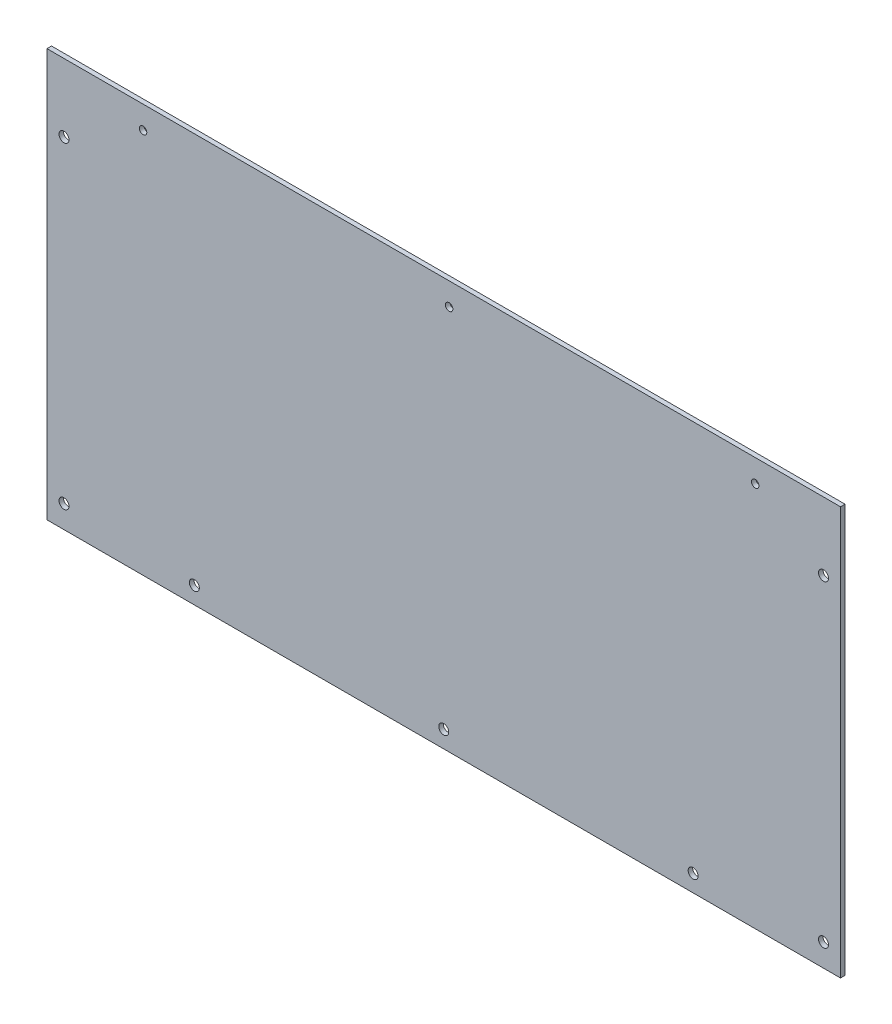
SolidWorks part; units mm, degrees
ref_plane "正面" through (0, 0, 0) normal (0, 0, 1) x (1, 0, 0)
ref_plane "平面" through (0, 0, 0) normal (0, 1, 0) x (1, 0, 0)
ref_plane "右側面" through (0, 0, 0) normal (1, 0, 0) x (0, 0, -1)
sketch "ｽｹｯﾁ1" plane through (0, 0, 0) normal (0, 0, 1) x (1, 0, 0)
  line L1 (-175, 90) -> (175, 90)
  line L2 (-175, 90) -> (-175, -90)
  line L3 (-175, -90) -> (175, -90)
  line L4 (175, 90) -> (175, -90)
  line L5 (-175, 90) -> (175, -90) construction
  line L6 (-175, -90) -> (175, 90) construction
  point P0 (0, 0)
  dimension "D1" = 350
  dimension "D2" = 180
extrude "ﾎﾞｽ - 押し出し1" add sketch "ｽｹｯﾁ1" along normal blind 2
sketch "ｽｹｯﾁ2" plane through (0, 0, 2) normal (0, 0, 1) x (1, 0, 0)
  line L0 (0, 0) -> (0, 80)
  line L1 (-175, 90) -> (-132.62, 90)
  line L2 (-175, 90) -> (-175, 80)
  line L3 (-175, 80) -> (-132.62, 80)
  line L4 (-132.62, 90) -> (-132.62, 80)
  line L5 (175, 90) -> (137.38, 90)
  line L6 (175, 90) -> (175, 80)
  line L7 (175, 80) -> (137.38, 80)
  line L8 (137.38, 90) -> (137.38, 80)
  circle A0 centre (-132.62, 80) radius 1
  circle A1 centre (137.38, 80) radius 1
  circle A2 centre (0, 80) radius 2.1
  dimension "D3" = 2
  dimension "D4" = 2
  dimension "D7" = 4.2
  dimension "D1" = 42.38
  dimension "D2" = 10
  dimension "D5" = 10
  dimension "D6" = 37.62
extrude "ｶｯﾄ - 押し出し1" cut sketch "ｽｹｯﾁ2" against normal blind 2 contours L3 A0 L4 | L4 A0 L3 | L7 A1 L8 | L8 A1 L7
sketch "ｽｹｯﾁ3" plane through (0, 0, 2) normal (0, 0, 1) x (1, 0, 0)
  line L0 (-175, -90) -> (-167.5, -90)
  line L1 (-175, -90) -> (175, -90) construction
  line L2 (-167.5, -90) -> (-167.5, -80)
  line L3 (-167.5, -80) -> (-167.5, 60)
  line L4 (175, -90) -> (167.5, -90)
  line L5 (167.5, -90) -> (167.5, -80)
  line L6 (167.5, -80) -> (167.5, 60)
  circle A0 centre (-167.5, 60) radius 2.2
  circle A1 centre (-167.5, -80) radius 2.2
  circle A2 centre (167.5, 60) radius 2.2
  circle A3 centre (167.5, -80) radius 2.2
  dimension "D5" = 4.4
  dimension "D8" = 4.4
  dimension "D9" = 4.4
  dimension "D10" = 4.4
  dimension "D1" = 7.5
  dimension "D2" = 7.5
  dimension "D3" = 10
  dimension "D4" = 140
  dimension "D6" = 10
  dimension "D7" = 140
extrude "ｶｯﾄ - 押し出し2" cut sketch "ｽｹｯﾁ3" against normal blind 160
sketch "ｽｹｯﾁ4" plane through (0, 0, 2) normal (0, 0, 1) x (1, 0, 0)
  line L0 (0, -90) -> (0, -82.5)
  line L1 (-175, -90) -> (175, -90) construction
  line L2 (0, -82.5) -> (110, -82.5)
  line L3 (0, -82.5) -> (-110, -82.5)
  circle A0 centre (-110, -82.5) radius 2.2
  circle A1 centre (0, -82.5) radius 2.2
  circle A2 centre (110, -82.5) radius 2.2
  dimension "D4" = 4.4
  dimension "D5" = 4.4
  dimension "D6" = 4.4
  dimension "D1" = 7.5
  dimension "D2" = 110
  dimension "D3" = 110
extrude "ｶｯﾄ - 押し出し3" cut sketch "ｽｹｯﾁ4" against normal blind 160
sketch "ｽｹｯﾁ5" plane through (0, 0, 2) normal (0, 0, 1) x (1, 0, 0)
  line L0 (137.38, 80) -> (2.38, 80)
  circle A0 centre (2.38, 80) radius 1
  dimension "D2" = 2
  dimension "D1" = 135
extrude "ｶｯﾄ - 押し出し4" cut sketch "ｽｹｯﾁ5" against normal blind 10
hole_wizard "M4x0.7 ねじ穴1" positions "3Dｽｹｯﾁ1" profile "ｽｹｯﾁ6" tap size "M4x0.7" standard "JIS" end condition through all
sketch3d "3Dｽｹｯﾁ1"
  line L0 (-132.62, 80, 0) -> (-132.62, 80, 2) construction
  line L1 (2.38, 80, 0) -> (2.38, 80, 2) construction
  line L2 (137.38, 80, 0) -> (137.38, 80, 2) construction
  point P0 (-132.62, 80, 2)
  point P4 (2.38, 80, 2)
  point P8 (137.38, 80, 2)
sketch "ｽｹｯﾁ6" plane through (-132.62, 80, 2) normal (1, 0, 0) x (0, -1, 0)
  line L0 (0, 0) -> (0, 2)
  line L1 (0, 2) -> (1.65, 2)
  line L2 (1.65, 2) -> (1.65, 0)
  line L5 (1.65, 0) -> (0, 0)
  line L11 (0, -6.35) -> (0, 107.95) construction
  dimension "次ｻｰﾌｪｽまでのねじ下穴ﾄﾞﾘﾙ直径" = 3.3
  dimension "次ｻｰﾌｪｽまでのねじ下穴ﾄﾞﾘﾙの深さ" = 2
cosmetic thread "穴のねじ山1" parameters "D2"=4
cosmetic thread "穴のねじ山2" parameters "D2"=4
cosmetic thread "穴のねじ山3" parameters "D2"=4
